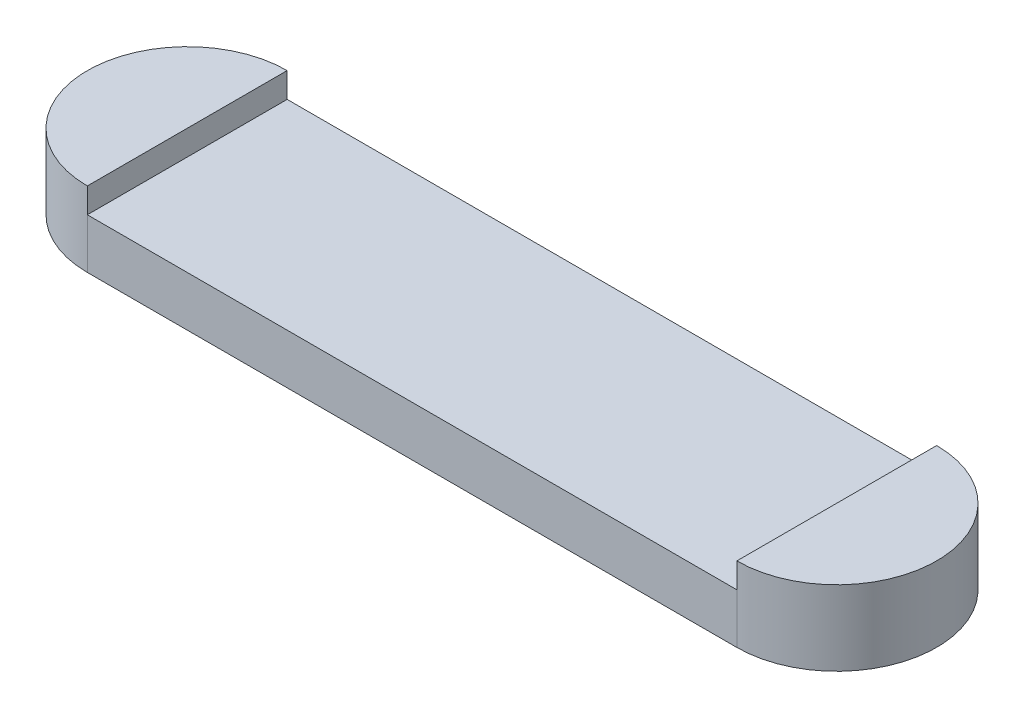
SolidWorks part; units mm, degrees
ref_plane "Front Plane" through (0, 0, 0) normal (0, 0, 1) x (1, 0, 0)
ref_plane "Top Plane" through (0, 0, 0) normal (0, 1, 0) x (1, 0, 0)
ref_plane "Right Plane" through (0, 0, 0) normal (1, 0, 0) x (0, 0, -1)
sketch "Sketch1" plane through (0, 0, 0) normal (0, 1, 0) x (1, 0, 0)
  line L0 (0, 0) -> (-26, 0) construction
  line L1 (0, -4) -> (-26, -4)
  line L2 (0, 4) -> (-26, 4)
  arc A0 (0, -4) -> (0, 4) centre (0, 0) ccw
  arc A1 (-26, 4) -> (-26, -4) centre (-26, 0) ccw
  point P3 (-13, 0)
  dimension "D1" = 26
  dimension "D2" = 4
extrude "Boss-Extrude1" add sketch "Sketch1" along normal blind 2
sketch "Sketch2" plane through (0, 2, 0) normal (0, 1, 0) x (1, 0, 0)
  line L0 (-26, 4) -> (-26, -4)
  line L1 (0, 4) -> (-26, 4) construction
  line L2 (0, 4) -> (0, -4)
  arc A0 (-26, 4) -> (-26, -4) centre (-26, 0) ccw construction
  arc A1 (-26, 4) -> (-30, 0) centre (-26, 0) ccw
  arc A2 (-30, 0) -> (-26, -4) centre (-26, 0) ccw
  arc A3 (0, -4) -> (0, 4) centre (0, 0) ccw construction
  arc A4 (0, 4) -> (0, -4) centre (0, 0) cw
extrude "Boss-Extrude2" add sketch "Sketch2" along normal blind 1
